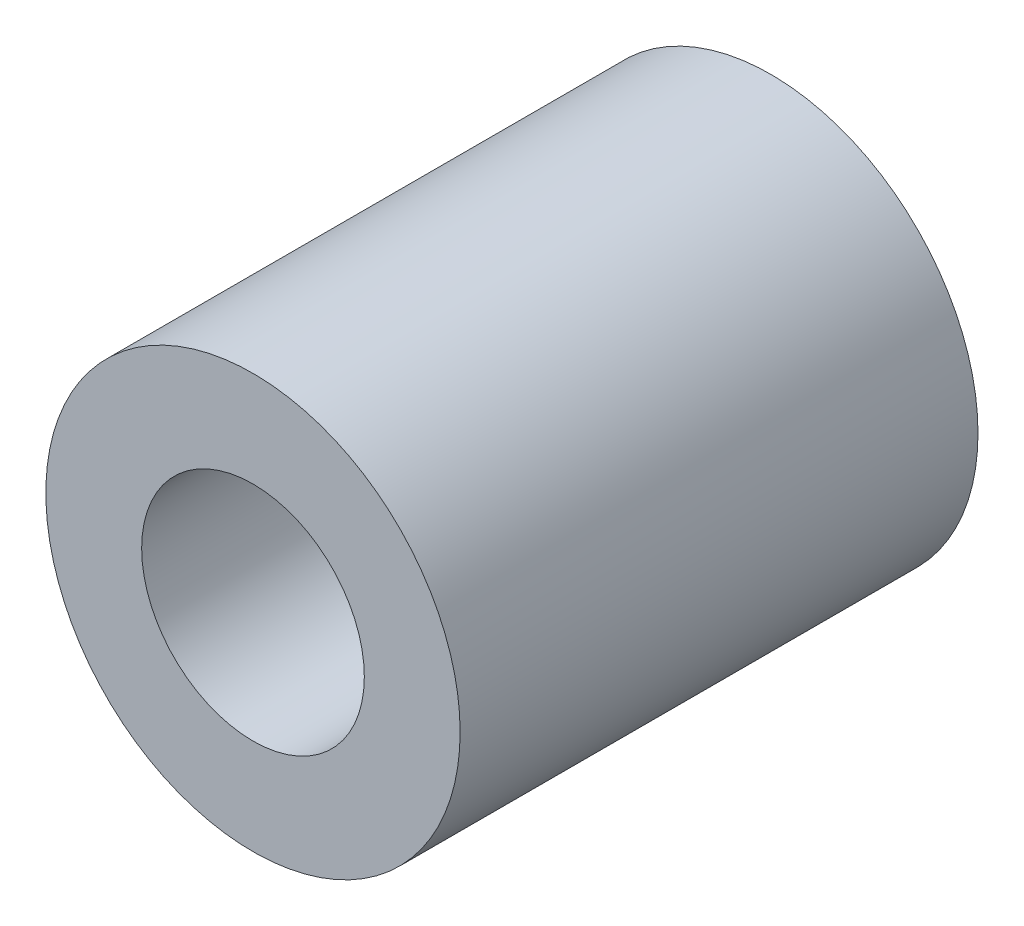
SolidWorks part; units mm, degrees
ref_plane "前基準面" through (0, 0, 0) normal (0, 0, 1) x (1, 0, 0)
ref_plane "上基準面" through (0, 0, 0) normal (0, 1, 0) x (1, 0, 0)
ref_plane "右基準面" through (0, 0, 0) normal (1, 0, 0) x (0, 0, -1)
sketch "草圖2" plane through (0, 0, 0) normal (0, 0, 1) x (1, 0, 0)
  circle A0 centre (0, 0) radius 4
  dimension "D1" = 8
extrude "填料-伸長1" add sketch "草圖2" along normal blind 10
hole_wizard "M4 餘隙孔1" positions "草圖3" profile "草圖4" hole size "M4" standard "Ansi Metric" end condition through all
sketch "草圖3" plane through (0, 0, 10) normal (0, 0, 1) x (1, 0, 0)
  point P0 (0, 0)
sketch "草圖4" plane through (0, 0, 10) normal (1, 0, 0) x (0, -1, 0)
  line L0 (0, 0) -> (0, 10)
  line L1 (0, 10) -> (2.15, 10)
  line L2 (2.15, 10) -> (2.15, 0)
  line L5 (2.15, 0) -> (0, 0)
  line L11 (0, -6.35) -> (0, 107.95) construction
  dimension "貫穿孔直徑" = 4.3
  dimension "貫穿孔深度" = 10
